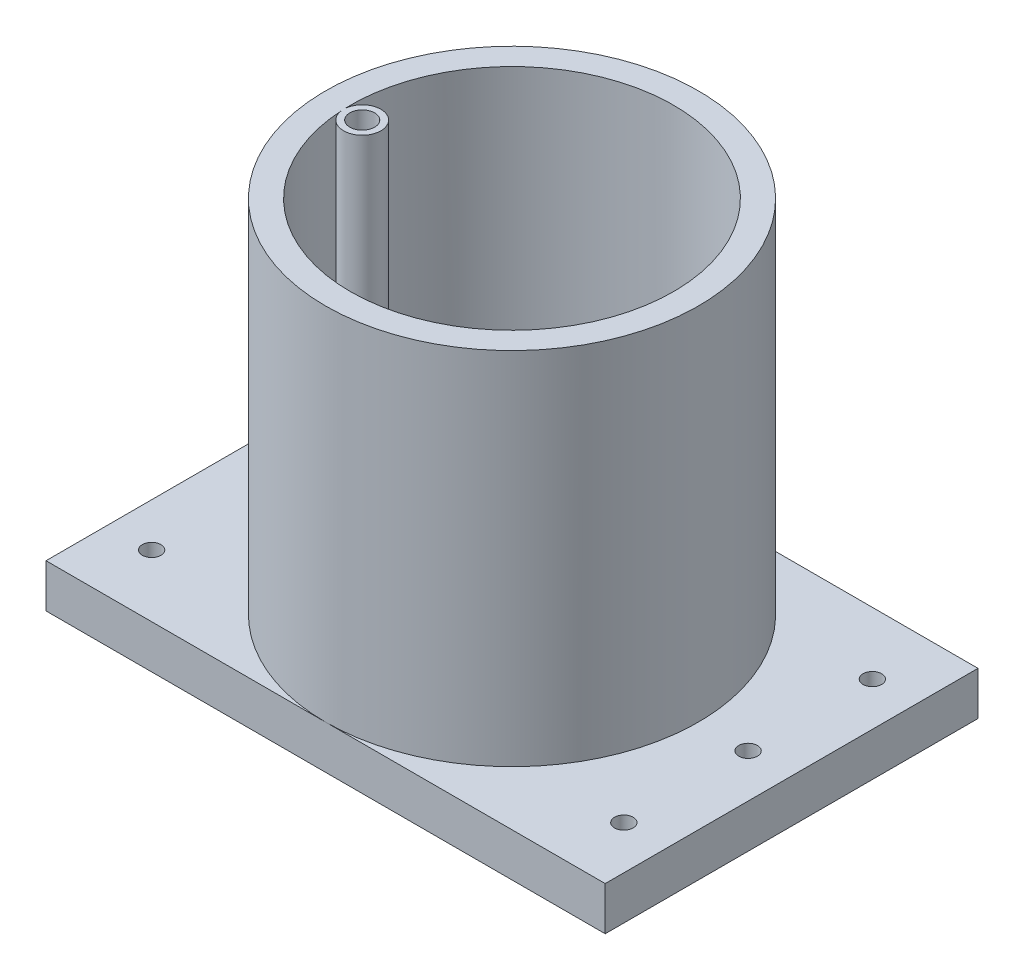
SolidWorks part; units mm, degrees
ref_plane "Front Plane" through (0, 0, 0) normal (0, 0, 1) x (1, 0, 0)
ref_plane "Top Plane" through (0, 0, 0) normal (0, 1, 0) x (1, 0, 0)
ref_plane "Right Plane" through (0, 0, 0) normal (1, 0, 0) x (0, 0, -1)
sketch "Çizim1" plane through (0, 0, 0) normal (0, 1, 0) x (1, 0, 0)
  circle A0 centre (0, 0) radius 30
extrude "Yükseklik-Ekstrüzyon1" add sketch "Çizim1" along normal blind 65
sketch "Çizim2" plane through (0, 65, 0) normal (0, 1, 0) x (1, 0, 0)
  circle A0 centre (0, 0) radius 26
extrude "Kes-Ekstrüzyon1" cut sketch "Çizim2" against normal blind 62
sketch "Çizim3" plane through (0, 3, 0) normal (0, 1, 0) x (1, 0, 0)
  circle A3 centre (-22.9755, -1.1294) radius 3
extrude "Yükseklik-Ekstrüzyon4" add sketch "Çizim3" along normal blind 52 from offset 10 contours A3
sketch "Çizim4" plane through (0, 65, 0) normal (0, 1, 0) x (1, 0, 0)
  circle A0 centre (-22.9755, -1.1294) radius 2
extrude "Kes-Ekstrüzyon2" cut sketch "Çizim4" against normal blind 52
sketch "Çizim5" plane through (0, 0, 0) normal (0, -1, 0) x (1, 0, 0)
  line L0 (0, 30) -> (-45, 30) construction
  line L1 (0, -30) -> (45, -30) construction
  line L3 (-45, 30) -> (45, 30)
  line L4 (-45, 30) -> (-45, -30)
  line L5 (-45, -30) -> (45, -30)
  line L6 (45, 30) -> (45, -30)
  circle A0 centre (0, 0) radius 30 construction
extrude "Yükseklik-Ekstrüzyon5" add sketch "Çizim5" against normal blind 7 contours L4 L3 L6 L5
sketch "Çizim6" plane through (0, 7, 0) normal (0, 1, 0) x (1, 0, 0)
  circle A0 centre (38, 0) radius 1.5
  circle A1 centre (-38, 0) radius 1.5
extrude "Kes-Ekstrüzyon3" cut sketch "Çizim6" against normal blind 10
sketch "Çizim7" plane through (0, 7, 0) normal (0, 1, 0) x (1, 0, 0)
  line L0 (-38, 0) -> (-38, 20) construction
  line L1 (-38, 0) -> (-38, -20) construction
  line L2 (38, 0) -> (38, 20) construction
  line L3 (38, 0) -> (38, -20) construction
  circle A0 centre (-38, 20) radius 1.5
  circle A1 centre (-38, -20) radius 1.5
  circle A2 centre (38, -20) radius 1.5
  circle A3 centre (38, 20) radius 1.5
extrude "Kes-Ekstrüzyon4" cut sketch "Çizim7" against normal blind 10
